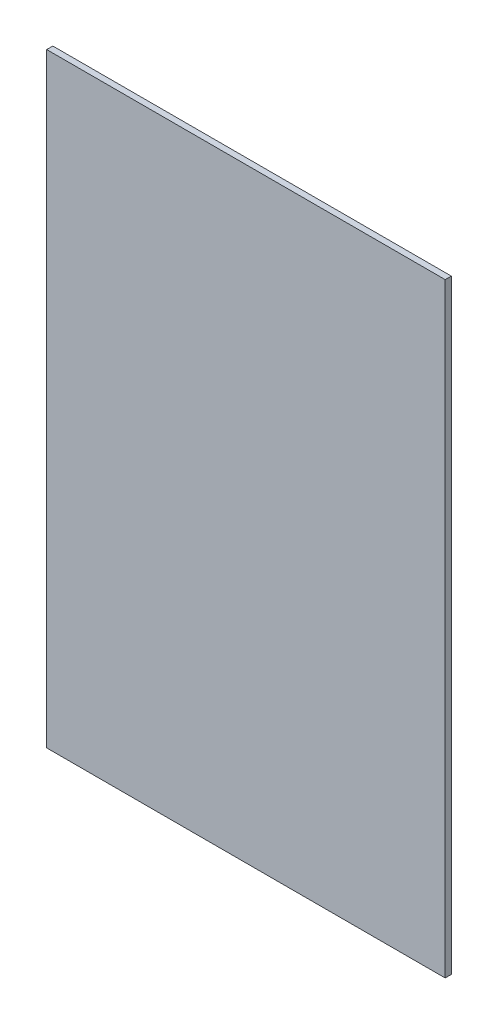
SolidWorks part; units mm, degrees
ref_plane "Спереди" through (0, 0, 0) normal (0, 0, 1) x (1, 0, 0)
ref_plane "Сверху" through (0, 0, 0) normal (0, 1, 0) x (1, 0, 0)
ref_plane "Справа" through (0, 0, 0) normal (1, 0, 0) x (0, 0, -1)
sketch "Sketch1" plane through (0, 0, 0) normal (0, 0, 1) x (1, 0, 0)
  line L0 (-110, 0) -> (-130, 0) construction
  line L5 (-130, 130) -> (130, 130)
  line L6 (-130, 130) -> (-130, -264.6)
  line L7 (-130, -264.6) -> (130, -264.6)
  line L8 (130, 130) -> (130, -264.6)
  line L9 (0, 110) -> (0, 130) construction
  line L10 (110, 0) -> (130, 0) construction
  line L12 (-19.4, -264.4) -> (-13.9, -264.4) construction
  circle A8 centre (0, 0) radius 110 construction
  circle A9 centre (0, 0) radius 110 construction
  circle A10 centre (0, 0) radius 110 construction
  circle A11 centre (0, 0) radius 110 construction
  dimension "D1" = 20
  dimension "D2" = 0.2
extrude "Extrude1" add sketch "Sketch1" along normal blind 4
equation "\"thickness\"=4"
equation "\"D1@Extrude1\"= \"thickness\""
equation "\"pin_l\"=5"
equation "\"pin_skew\"=4"
equation "\"pin_r\"=5"
equation "\"M4_plastic_thread\"=3.8"
equation "\"M3_plastic_thread\" = 2.8"
equation "\"min_d\"=0.2"
equation "\"D2@Sketch1\"=\"min_d\""
